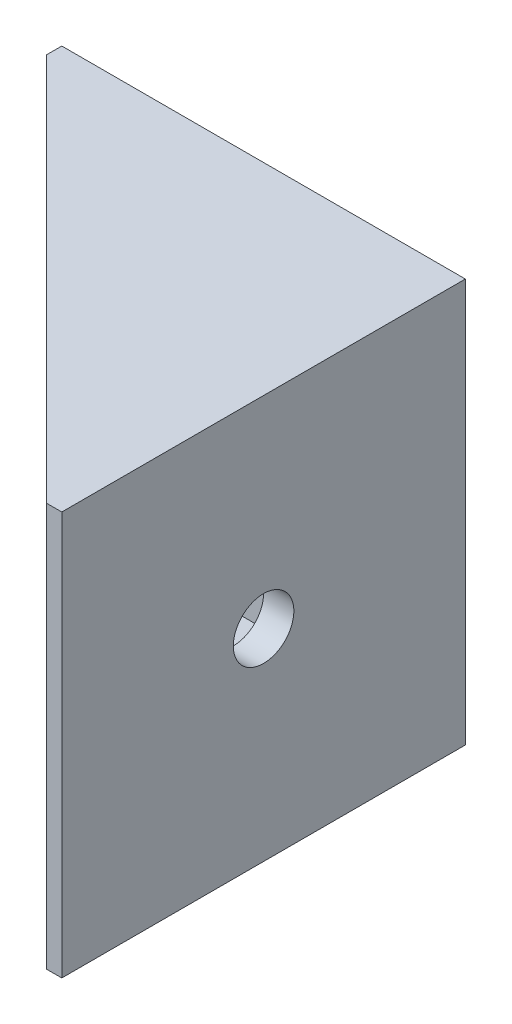
SolidWorks part; units mm, degrees
ref_plane "Ebene vorne" through (0, 0, 0) normal (0, 0, 1) x (1, 0, 0)
ref_plane "Ebene oben" through (0, 0, 0) normal (0, 1, 0) x (1, 0, 0)
ref_plane "Ebene rechts" through (0, 0, 0) normal (1, 0, 0) x (0, 0, -1)
sketch "Sketch2" plane through (0, 0, 0) normal (0, 1, 0) x (1, 0, 0)
  line L0 (0, 0) -> (-40, 0)
  line L1 (-40, 0) -> (-40, -1.5)
  line L2 (-40, -1.5) -> (-38.5, -3)
  line L3 (-38.5, -3) -> (-3, -3)
  line L4 (-3, -3) -> (-3, -38.5)
  line L5 (-3, -38.5) -> (-1.5, -40)
  line L6 (-1.5, -40) -> (0, -40)
  line L7 (0, -40) -> (0, 0)
  dimension "D1" = 3
  dimension "D2" = 3
  dimension "D3" = 40
  dimension "D4" = 40
  dimension "D5" = 135
  dimension "D6" = 1.5
  dimension "D7" = 1.5
  dimension "D8" = 135
extrude "Boss-Extrude1" add sketch "Sketch2" along normal mid plane 40
sketch "Sketch3" plane through (0, 0, 3) normal (0, 0, 1) x (1, 0, 0)
  line L0 (-38.5, 20) -> (-3, 20) construction
  circle A0 centre (-20, 0) radius 3
  dimension "D1" = 6
  dimension "D2" = 20
  dimension "D3" = 20
extrude "Cut-Extrude1" cut sketch "Sketch3" against normal mid plane 40
sketch "Sketch4" plane through (-3, 0, 0) normal (-1, 0, 0) x (0, 0, 1)
  line L0 (0, 20) -> (0, -20) construction
  line L2 (3, 20) -> (38.5, 20) construction
  circle A0 centre (20, 0) radius 3
  point P6 (15.3744, 20)
  dimension "D1" = 6
  dimension "D2" = 20
  dimension "D3" = 20
extrude "Cut-Extrude2" cut sketch "Sketch4" against normal mid plane 40
sketch "Sketch5" plane through (0, -20, 0) normal (0, -1, 0) x (1, 0, 0)
  line L0 (-38.5, 3) -> (-3, 38.5)
  line L1 (-3, 38.5) -> (-3, 3)
  line L2 (-3, 3) -> (-38.5, 3)
extrude "Boss-Extrude2" add sketch "Sketch5" against normal blind 3
mirror "Mirror1" about plane through (0, 0, 0) normal (0, 1, 0) of "Boss-Extrude2"
